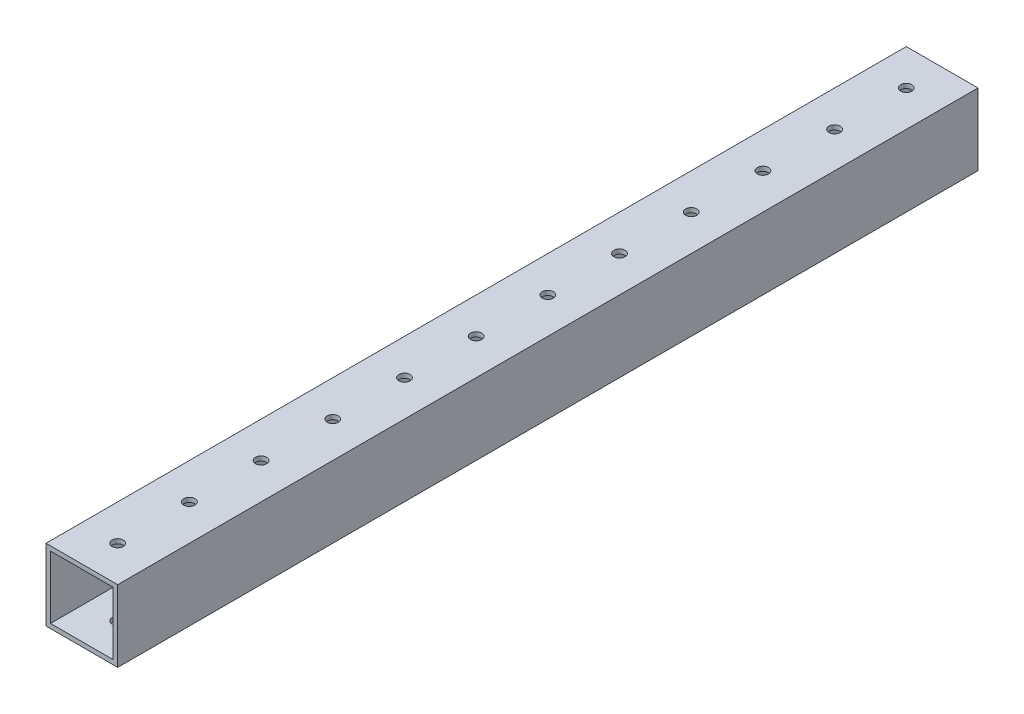
SolidWorks part; units mm, degrees
ref_plane "Front Plane" through (0, 0, 0) normal (0, 0, 1) x (1, 0, 0)
ref_plane "Top Plane" through (0, 0, 0) normal (0, 1, 0) x (1, 0, 0)
ref_plane "Right Plane" through (0, 0, 0) normal (1, 0, 0) x (0, 0, -1)
sketch "Sketch1" plane through (0, 0, 0) normal (0, 0, 1) x (1, 0, 0)
  line L1 (-11.1125, 11.1125) -> (11.1125, 11.1125)
  line L2 (-11.1125, 11.1125) -> (-11.1125, -11.1125)
  line L3 (-11.1125, -11.1125) -> (11.1125, -11.1125)
  line L4 (11.1125, 11.1125) -> (11.1125, -11.1125)
  line L5 (-11.1125, 11.1125) -> (11.1125, -11.1125) construction
  line L6 (-11.1125, -11.1125) -> (11.1125, 11.1125) construction
  line L7 (-12.7, 12.7) -> (12.7, 12.7)
  line L8 (-12.7, 12.7) -> (-12.7, -12.7)
  line L9 (-12.7, -12.7) -> (12.7, -12.7)
  line L10 (12.7, 12.7) -> (12.7, -12.7)
  line L11 (-12.7, 12.7) -> (12.7, -12.7) construction
  line L12 (-12.7, -12.7) -> (12.7, 12.7) construction
  point P0 (0, 0)
  point P6 (0, 0)
  dimension "D1" = 25.4
  dimension "D2" = 25.4
  dimension "D3" = 1.5875
extrude "Boss-Extrude1" add sketch "Sketch1" along normal blind 304.8
sketch "Sketch2" plane through (0, 12.7, 0) normal (0, 1, 0) x (1, 0, 0)
  line L0 (0, -304.8) -> (0, -292.1) construction
  line L1 (12.7, -304.8) -> (-12.7, -304.8) construction
  circle A0 centre (0, -292.1) radius 1.9844
  circle A1 centre (0, -266.7) radius 1.9844
  circle A2 centre (0, -241.3) radius 1.9844
  circle A3 centre (0, -215.9) radius 1.9844
  circle A4 centre (0, -190.5) radius 1.9844
  circle A5 centre (0, -165.1) radius 1.9844
  circle A6 centre (0, -139.7) radius 1.9844
  circle A7 centre (0, -114.3) radius 1.9844
  circle A8 centre (0, -88.9) radius 1.9844
  circle A9 centre (0, -63.5) radius 1.9844
  circle A10 centre (0, -38.1) radius 1.9844
  circle A11 centre (0, -12.7) radius 1.9844
  dimension "D2" = 3.9688
  dimension "D1" = 12.7
  dimension "D3" = 12
extrude "Cut-Extrude1" cut sketch "Sketch2" against normal through all
